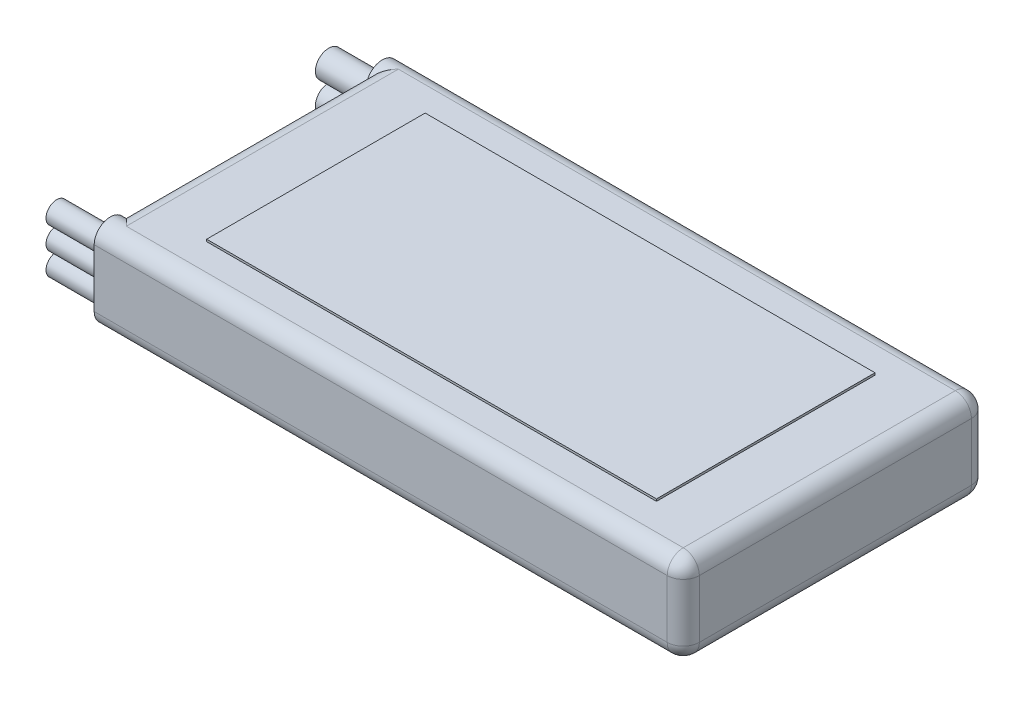
SolidWorks part; units mm, degrees
ref_plane "Front Plane" through (0, 0, 0) normal (0, 0, 1) x (1, 0, 0)
ref_plane "Top Plane" through (0, 0, 0) normal (0, 1, 0) x (1, 0, 0)
ref_plane "Right Plane" through (0, 0, 0) normal (1, 0, 0) x (0, 0, -1)
sketch "Sketch1" plane through (0, 0, 0) normal (0, 1, 0) x (1, 0, 0)
  line L1 (-26.5251, 23.1598) -> (43.3249, 23.1598)
  line L2 (-26.5251, 23.1598) -> (-26.5251, -12.9082)
  line L3 (-26.5251, -12.9082) -> (43.3249, -12.9082)
  line L4 (43.3249, 23.1598) -> (43.3249, -12.9082)
  dimension "D1" = 69.85
  dimension "D2" = 36.068
extrude "Battery" add sketch "Sketch1" along normal blind 10.668
fillet "Fillet" radius 1.905 12 edges at (43.3249, 5.334, 12.9082) (8.3999, 0, 12.9082) (43.3249, 0, -5.1258) (-26.5251, 5.334, 12.9082) (-26.5251, 0, -5.1258) (43.3249, 5.334, -23.1598) (-26.5251, 5.334, -23.1598) (8.3999, 0, -23.1598) (8.3999, 10.668, -23.1598) (43.3249, 10.668, -5.1258) (8.3999, 10.668, 12.9082) (-26.5251, 10.668, -5.1258)
sketch "Sketch2" plane through (-26.5251, 0, 0) normal (-1, 0, 0) x (0, 0, 1)
  line L0 (11.0032, 8.763) -> (11.0032, 1.905) construction
  line L1 (12.9082, 8.763) -> (12.9082, 1.905)
  line L2 (9.0982, 8.763) -> (9.0982, 1.905)
  line L3 (12.9082, 8.763) -> (12.9082, 1.905) construction
  line L4 (-21.2548, 8.763) -> (-21.2548, 1.905) construction
  line L5 (-19.3498, 8.763) -> (-19.3498, 1.905)
  line L6 (-23.1598, 8.763) -> (-23.1598, 1.905)
  line L7 (-23.1598, 1.905) -> (-23.1598, 8.763) construction
  arc A0 (12.9082, 8.763) -> (9.0982, 8.763) centre (11.0032, 8.763) ccw
  arc A1 (9.0982, 1.905) -> (12.9082, 1.905) centre (11.0032, 1.905) ccw
  arc A2 (-19.3498, 8.763) -> (-23.1598, 8.763) centre (-21.2548, 8.763) ccw
  arc A3 (-23.1598, 1.905) -> (-19.3498, 1.905) centre (-21.2548, 1.905) ccw
  point P4 (11.0032, 5.334)
  point P15 (-21.2548, 5.334)
extrude "Wire Boss" add sketch "Sketch2" against normal blind 5.08
sketch "Sketch3" plane through (-26.5251, 0, 0) normal (-1, 0, 0) x (0, 0, 1)
  line L0 (-21.2548, 10.668) -> (-21.2548, 7.112) construction
  line L1 (-21.2548, 7.112) -> (-21.2548, 3.556) construction
  line L2 (-21.2548, 3.556) -> (-21.2548, 0) construction
  line L3 (11.0032, 10.668) -> (11.0032, 8.001) construction
  line L4 (11.0032, 8.001) -> (11.0032, 5.334) construction
  line L5 (11.0032, 5.334) -> (11.0032, 2.667) construction
  line L6 (11.0032, 2.667) -> (11.0032, 0) construction
  arc A4 (-19.3498, 8.763) -> (-23.1598, 8.763) centre (-21.2548, 8.763) ccw construction
  arc A5 (-23.1598, 1.905) -> (-19.3498, 1.905) centre (-21.2548, 1.905) ccw construction
  arc A6 (12.9082, 8.763) -> (9.0982, 8.763) centre (11.0032, 8.763) ccw construction
  arc A7 (9.0982, 1.905) -> (12.9082, 1.905) centre (11.0032, 1.905) ccw construction
  circle A8 centre (11.0032, 8.001) radius 1.27
  circle A9 centre (11.0032, 5.334) radius 1.27
  circle A10 centre (11.0032, 2.667) radius 1.27
  circle A11 centre (-21.2548, 7.112) radius 1.5875
  circle A12 centre (-21.2548, 3.556) radius 1.5875
  point P0 (11.0032, 8.001)
  point P1 (11.0032, 5.334)
  point P2 (11.0032, 2.667)
  point P3 (-21.2548, 7.112)
  point P4 (-21.2548, 3.556)
  dimension "D1" = 2.54
  dimension "D2" = 3.175
extrude "Wires" add sketch "Sketch3" along normal blind 6.35
sketch "Sketch4" plane through (0, 10.668, 0) normal (0, 1, 0) x (1, 0, 0)
  line L0 (-24.6201, -11.0032) -> (41.4199, -11.0032) construction
  line L1 (35.0699, -7.8282) -> (-18.2701, -7.8282)
  line L2 (35.0699, -7.8282) -> (35.0699, 18.0798)
  line L3 (35.0699, 18.0798) -> (-18.2701, 18.0798)
  line L4 (-18.2701, -7.8282) -> (-18.2701, 18.0798)
  line L5 (41.4199, 21.2548) -> (-24.6201, 21.2548) construction
  line L6 (41.4199, -11.0032) -> (41.4199, 21.2548) construction
  line L7 (-24.6201, 21.2548) -> (-24.6201, -11.0032) construction
  dimension "D1" = 3.175
  dimension "D2" = 3.175
  dimension "D3" = 6.35
  dimension "D4" = 6.35
extrude "Label" add sketch "Sketch4" along normal blind 0.254
